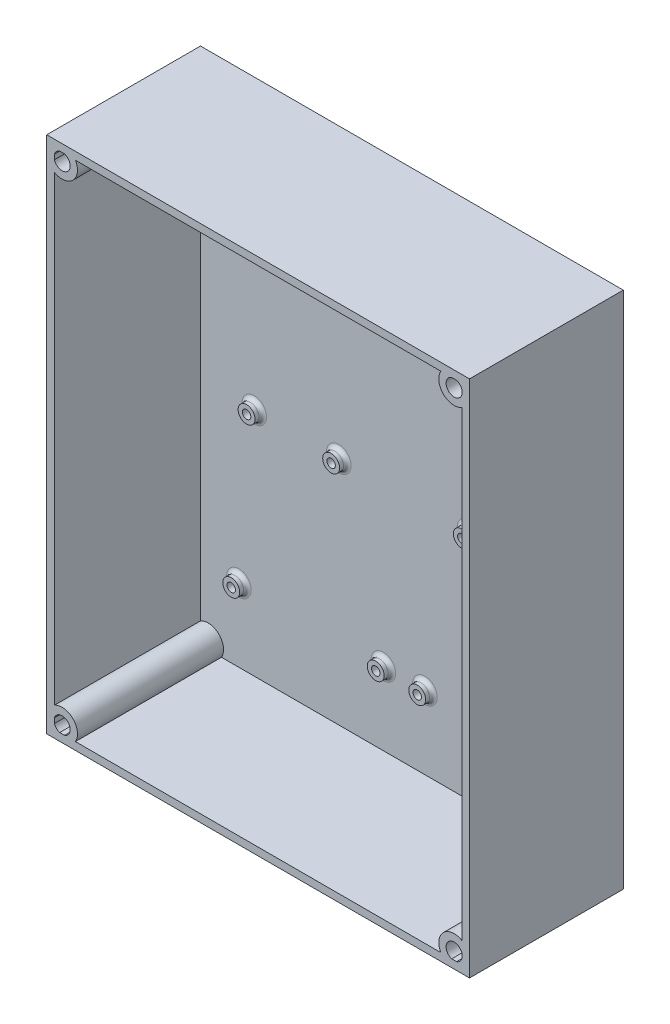
SolidWorks part; units mm, degrees
ref_plane "Front Plane" through (0, 0, 0) normal (0, 0, 1) x (1, 0, 0)
ref_plane "Top Plane" through (0, 0, 0) normal (0, 1, 0) x (1, 0, 0)
ref_plane "Right Plane" through (0, 0, 0) normal (1, 0, 0) x (0, 0, -1)
sketch "Sketch1" plane through (0, 0, 0) normal (0, 0, 1) x (1, 0, 0)
  line L1 (0, 0) -> (-139.7, 0)
  line L2 (0, 0) -> (0, 171.45)
  line L3 (0, 171.45) -> (-139.7, 171.45)
  line L4 (-139.7, 0) -> (-139.7, 171.45)
  dimension "D1" = 171.45
  dimension "D2" = 139.7
extrude "Boss-Extrude1" add sketch "Sketch1" along normal blind 50.8
shell "Shell2" thickness 2.54
sketch "Sketch3" plane through (0, 0, 50.8) normal (0, 0, 1) x (1, 0, 0)
  line L0 (-139.7, 85.725) -> (-127.386, 85.725) construction
  line L1 (-139.7, 171.45) -> (-139.7, 0) construction
  line L2 (-69.85, 0) -> (-69.85, 17.4636) construction
  line L3 (-139.7, 0) -> (0, 0) construction
  circle A0 centre (-134.62, 5.08) radius 2.667
  circle A1 centre (-134.62, 166.37) radius 2.667
  circle A2 centre (-5.08, 166.37) radius 2.667
  circle A3 centre (-5.08, 5.08) radius 2.667
  circle A4 centre (-134.62, 5.08) radius 5.08
  circle A5 centre (-134.62, 166.37) radius 5.08
  circle A6 centre (-5.08, 166.37) radius 5.08
  circle A7 centre (-5.08, 5.08) radius 5.08
  dimension "D1" = 5.334
  dimension "D2" = 5.08
  dimension "D3" = 5.08
  dimension "D4" = 10.16
extrude "Boss-Extrude3" add sketch "Sketch3" against normal blind 50.8
sketch "Sketch4" plane through (0, 0, 2.54) normal (0, 0, 1) x (1, 0, 0)
  line L0 (0, 0) -> (0, 171.45) construction
  line L1 (-10.16, 2.54) -> (-68.072, 2.54) construction
  line L2 (-10.16, 2.54) -> (-10.16, 82.296) construction
  line L3 (-10.16, 82.296) -> (-68.072, 82.296) construction
  line L4 (-68.072, 2.54) -> (-68.072, 82.296) construction
  line L5 (-139.7, 0) -> (0, 0) construction
  line L6 (-130.2206, 2.54) -> (-9.4794, 2.54) construction
  line L7 (-130.2206, 2.54) -> (-9.4794, 2.54) construction
  line L8 (-69.85, 2.54) -> (-69.85, 14.825) construction
  line L9 (-71.628, 2.54) -> (-71.628, 82.296) construction
  line L10 (-129.54, 82.296) -> (-71.628, 82.296) construction
  line L11 (-129.54, 2.54) -> (-129.54, 82.296) construction
  line L12 (-129.54, 2.54) -> (-71.628, 2.54) construction
  circle A0 centre (-62.992, 26.67) radius 1.397
  circle A1 centre (-15.24, 26.67) radius 1.397
  circle A2 centre (-48.26, 78.74) radius 1.397
  circle A3 centre (-20.32, 78.74) radius 1.397
  circle A4 centre (-119.38, 78.74) radius 1.397
  circle A5 centre (-91.44, 78.74) radius 1.397
  circle A6 centre (-124.46, 26.67) radius 1.397
  circle A7 centre (-76.708, 26.67) radius 1.397
  circle A8 centre (-62.992, 26.67) radius 2.794
  circle A9 centre (-48.26, 78.74) radius 2.794
  circle A10 centre (-20.32, 78.74) radius 2.794
  circle A11 centre (-15.24, 26.67) radius 2.794
  circle A12 centre (-76.708, 26.67) radius 2.794
  circle A13 centre (-91.44, 78.74) radius 2.794
  circle A14 centre (-119.38, 78.74) radius 2.794
  circle A15 centre (-124.46, 26.67) radius 2.794
  dimension "D5" = 24.13
  dimension "D6" = 24.13
  dimension "D7" = 5.08
  dimension "D8" = 5.08
  dimension "D9" = 2.794
  dimension "D10" = 2.794
  dimension "D12" = 76.2
  dimension "D13" = 2.794
  dimension "D14" = 2.794
  dimension "D15" = 10.16
  dimension "D16" = 38.1
  dimension "D17" = 5.588
  dimension "D18" = 5.588
  dimension "D19" = 5.588
  dimension "D20" = 5.588
  dimension "D21" = 5.588
  dimension "D22" = 5.588
  dimension "D23" = 5.588
  dimension "D24" = 5.588
  dimension "D1" = 79.756
  dimension "D2" = 57.912
  dimension "D3" = 10.16
  dimension "D4" = 2.54
  dimension "D11" = 76.2
extrude "Boss-Extrude4" add sketch "Sketch4" along normal blind 2.54
fillet "Fillet1" radius 1.27 8 edges at (-12.446, 26.67, 2.54) (-17.526, 78.74, 2.54) (-45.466, 78.74, 2.54) (-60.198, 26.67, 2.54) (-73.914, 26.67, 2.54) (-88.646, 78.74, 2.54) (-116.586, 78.74, 2.54) (-121.666, 26.67, 2.54)
